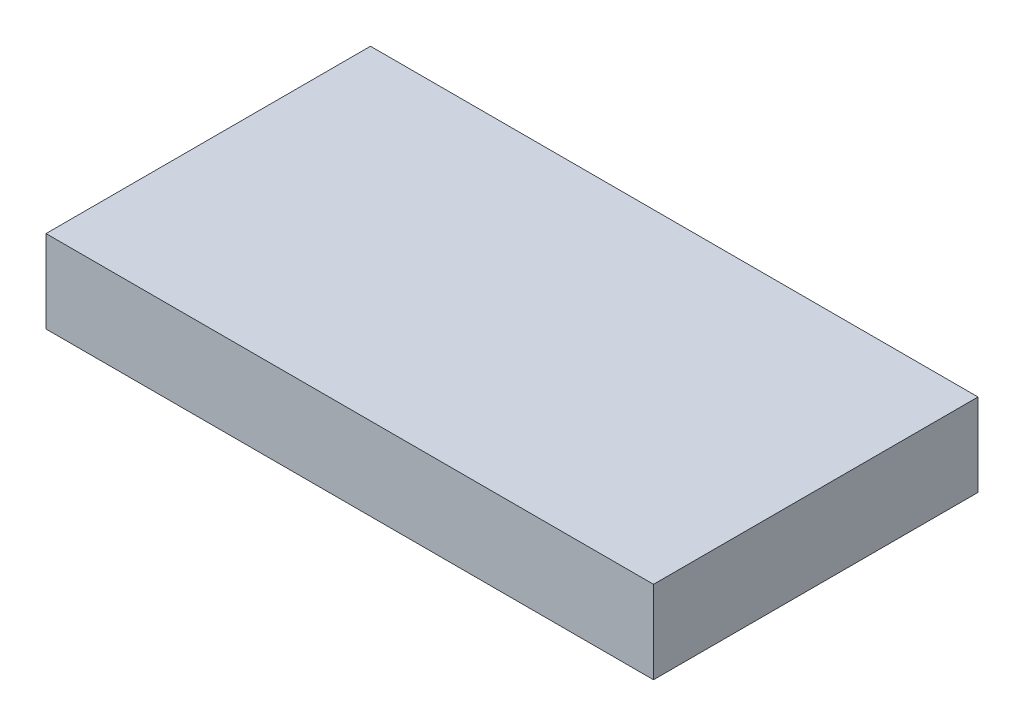
SolidWorks part; units mm, degrees
ref_plane "Front Plane" through (0, 0, 0) normal (0, 0, 1) x (1, 0, 0)
ref_plane "Top Plane" through (0, 0, 0) normal (0, 1, 0) x (1, 0, 0)
ref_plane "Right Plane" through (0, 0, 0) normal (1, 0, 0) x (0, 0, -1)
sketch "Sketch1" plane through (0, 0, 0) normal (0, 1, 0) x (1, 0, 0)
  line L1 (0, 0) -> (28.14, 0)
  line L2 (0, 0) -> (0, -15.03)
  line L3 (0, -15.03) -> (28.14, -15.03)
  line L4 (28.14, 0) -> (28.14, -15.03)
  dimension "D1" = 28.14
  dimension "D2" = 15.03
extrude "Boss-Extrude1" add sketch "Sketch1" along normal blind 3.83
